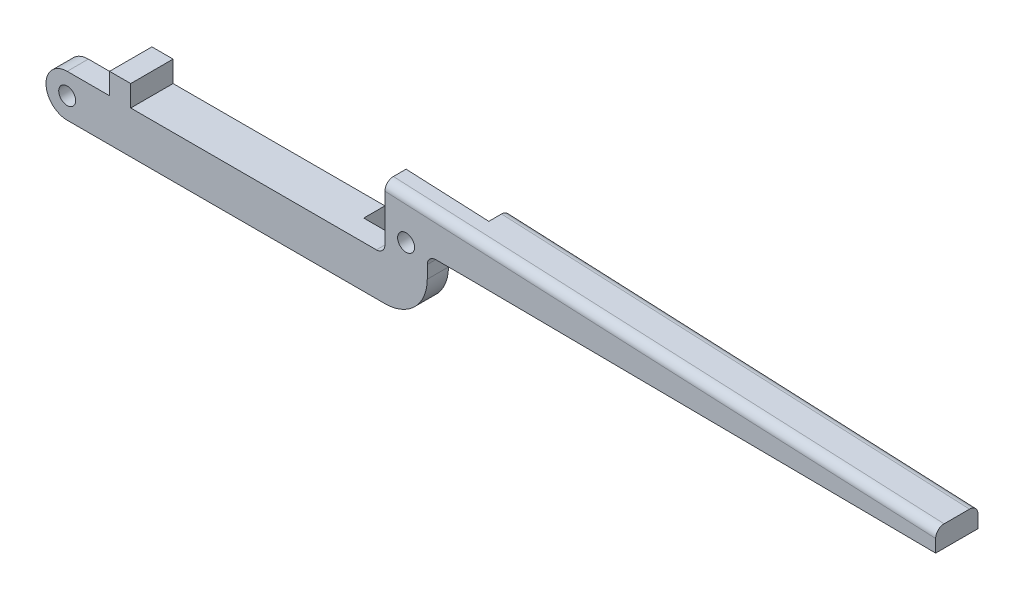
SolidWorks part; units mm, degrees
material "ABS"
ref_plane "Front Plane" through (0, 0, 0) normal (0, 0, 1) x (1, 0, 0)
ref_plane "Top Plane" through (0, 0, 0) normal (0, 1, 0) x (1, 0, 0)
ref_plane "Right Plane" through (0, 0, 0) normal (1, 0, 0) x (0, 0, -1)
sketch "Sketch1" plane through (0, 0, 0) normal (0, 0, 1) x (1, 0, 0)
  line L0 (0, 0) -> (22.5, 0) construction
  line L1 (0, -1.25) -> (0, -3.75)
  line L2 (0, -3.75) -> (20, -3.75)
  line L3 (20, 0) -> (20, 2.5)
  line L4 (-979.3777, 1.25) -> (22.9348, 1.25) construction
  line L8 (22.5, 0) -> (22.5, -3.75)
  line L9 (0, -1.25) -> (20, -1.25)
  line L10 (20, -1.25) -> (20, 0)
  line L11 (20, -3.75) -> (22.5, -3.75)
  line L12 (50, 1.25) -> (1066.376, 1.25) construction
  line L13 (22.5, 0) -> (50, 0) construction
  line L14 (22.5, 1.25) -> (50, 1.25) construction
  line L15 (22.5, 0) -> (52.5, 0)
  line L16 (52.5, 0) -> (52.5, 1)
  line L17 (52.5, 1) -> (20, 2.5)
  point P1 (0, -1.25)
  point P2 (20, 1.25)
  point P4 (0, 1.25)
  point P10 (52.5, 0)
  point P14 (52.5, 1)
  point P15 (22.5, 1.25)
  point P22 (20, 2.5)
  dimension "D1" = 1.25
  dimension "D2" = 1.25
  dimension "D3" = 2.5
  dimension "D4" = 20
  dimension "D5" = 30
  dimension "D6" = 1.25
  dimension "D7" = 2.5
  dimension "D8" = 1
  dimension "D9" = 2.5
  dimension "D10" = 5
extrude "Boss-Extrude1" add sketch "Sketch1" along normal blind 2.5
sketch "Sketch2" plane through (0, 0, 2.5) normal (0, 0, 1) x (1, 0, 0)
  line L0 (0, -3.75) -> (22.5, -3.75) construction
  line L1 (22.5, -3.75) -> (20, -3.75)
  line L2 (22.5, -3.75) -> (22.5, 2.5)
  line L3 (22.5, 2.5) -> (20, 2.5)
  line L4 (20, -3.75) -> (20, 2.5)
  line L5 (0, -1.25) -> (2.5, -1.25)
  line L6 (0, -1.25) -> (0, -3.75)
  line L7 (0, -3.75) -> (2.5, -3.75)
  line L8 (2.5, -1.25) -> (2.5, -3.75)
  dimension "D1" = 2.5
extrude "Cut-Extrude1" cut sketch "Sketch2" against normal blind 1.25
sketch "Sketch3" plane through (0, 0, 1.25) normal (0, 0, 1) x (1, 0, 0)
  line L0 (0, -1.25) -> (0, -3.75) construction
  line L1 (2.5, -1.25) -> (0, -1.25) construction
  line L2 (20, 2.5) -> (20, -1.25) construction
  line L3 (20, -3.75) -> (22.5, -3.75) construction
  circle A0 centre (1.25, -2.5) radius 0.5
  circle A1 centre (21.25, 0) radius 0.5
  point P0 (0, -2.5)
  point P1 (1.25, -1.25)
  point P4 (1.25, -2.5)
  point P9 (20, 0)
  point P10 (21.25, 0)
  dimension "D1" = 1
  dimension "D6" = 1
  dimension "D2" = 1.25
  dimension "D3" = 3.75
  dimension "D4" = 1.25
  dimension "D5" = 1.25
extrude "Cut-Extrude2" cut sketch "Sketch3" against normal through all
sketch "Sketch4" plane through (0, 0, 1.25) normal (0, 0, 1) x (1, 0, 0)
  line L1 (0, -3.75) -> (2.5, -3.75)
  line L2 (0, -3.75) -> (0, -1.25)
  line L3 (0, -1.25) -> (2.5, -1.25)
  line L4 (2.5, -3.75) -> (2.5, -1.25)
  line L5 (20, -3.75) -> (22.5, -3.75)
  line L6 (20, -3.75) -> (20, 2.3846)
  line L7 (20, 2.3846) -> (22.5, 2.3846)
  line L8 (22.5, -3.75) -> (22.5, 2.3846)
  circle A0 centre (1.25, -2.5) radius 0.5
  circle A1 centre (21.25, 0) radius 0.5
extrude "Boss-Extrude2" add sketch "Sketch4" along normal up to surface (1.25 mm away) up to face at (11.25, -2.5, 2.5)
sketch "Sketch5" plane through (0, 0, 1.25) normal (0, 0, 1) x (1, 0, 0)
  line L0 (20, 2.3846) -> (20, 2.5)
  line L1 (20, 2.5) -> (22.5, 2.3846)
  line L2 (22.5, 2.3846) -> (20, 2.3846)
extrude "Boss-Extrude3" add sketch "Sketch5" along normal blind 1.25
sketch "Sketch6" plane through (0, 0, 0) normal (0, 0, -1) x (-1, 0, 0)
  line L0 (-20, -1.25) -> (0, -1.25) construction
  line L1 (-22.5, -3.75) -> (-20, -3.75)
  line L2 (-22.5, -3.75) -> (-22.5, 2.5)
  line L3 (-22.5, 2.5) -> (-20, 2.5)
  line L4 (-20, -3.75) -> (-20, 2.5)
  line L5 (0, -3.75) -> (-2.5, -3.75)
  line L6 (0, -3.75) -> (0, -1.25)
  line L7 (0, -1.25) -> (-2.5, -1.25)
  line L8 (-2.5, -3.75) -> (-2.5, -1.25)
  dimension "D1" = 2.5
extrude "Cut-Extrude3" cut sketch "Sketch6" against normal blind 1.25
sketch "Sketch7" plane through (0, 0, 0) normal (0, 0, -1) x (-1, 0, 0)
  line L0 (-2.5, -1.25) -> (-2.5, -3.75) construction
  line L1 (-2.5, -3.75) -> (-2.5, -1.25)
  arc A0 (-2.5, -1.25) -> (-2.5, -3.75) centre (-2.5, -2.5) ccw
extrude "Cut-Extrude4" cut sketch "Sketch7" against normal blind 1.25
sketch "Sketch9" plane through (0, 0, 1.25) normal (0, 0, -1) x (-1, 0, 0)
  line L0 (-1.25, -1.25) -> (0, -1.25)
  line L1 (0, -1.25) -> (0, -3.75)
  line L2 (0, -3.75) -> (-1.25, -3.75)
  arc A0 (-1.25, -3.75) -> (-1.25, -1.25) centre (-1.25, -2.5) ccw
  line M2 (0, -3.75) -> (0, -1.25)
  line M3 (0, -1.25) -> (-2.5, -1.25)
  line M5 (-2.5, -3.75) -> (0, -3.75)
extrude "Cut-Extrude5" cut sketch "Sketch9" against normal blind 1.25 contours A0 L1 M3 | A0 M5 M2
sketch "Sketch10" plane through (0, 0, 0) normal (0, 0, -1) x (-1, 0, 0)
  line L0 (-22.5, 2.3846) -> (-24.8821, 2.2747)
  line L1 (-52.5, 1) -> (-22.5, 2.3846) construction
  line L2 (-22.5, 2.3846) -> (-22.5, 0)
  line L3 (-20, -3.75) -> (-20, -1.25)
  line L4 (-20, -1.25) -> (-17.5, -1.25)
  arc A0 (-24.8821, 2.2747) -> (-22.5, 0) centre (-22.5, 2.3846) ccw
  arc A1 (-20, -3.75) -> (-17.5, -1.25) centre (-20, -1.25) ccw
extrude "Cut-Extrude6" cut sketch "Sketch10" against normal blind 1.25
sketch "Sketch11" plane through (0, 0, 1.25) normal (0, 0, -1) x (-1, 0, 0)
  line L0 (-22.5, 0) -> (-22.5, -3.75) construction
  line L1 (-22.5, -1.25) -> (-22.5, -3.75)
  line L2 (-22.5, -3.75) -> (-20, -3.75)
  arc A0 (-22.5, -1.25) -> (-20, -3.75) centre (-20, -1.25) ccw
  point P0 (-20, -1.25)
  point P1 (-22.5, -1.25)
extrude "Cut-Extrude7" cut sketch "Sketch11" against normal blind 1.25
sketch "Sketch12" plane through (0, 0, 0) normal (0, 0, -1) x (-1, 0, 0)
  line L0 (-24.8821, 2.2747) -> (-24.8821, 0)
  line L1 (-22.5, 0) -> (-52.5, 0) construction
  line L2 (-24.8821, 0) -> (-22.5, 0)
  arc A0 (-22.5, 0) -> (-24.8821, 2.2747) centre (-22.5, 2.3846) cw
extrude "Cut-Extrude8" cut sketch "Sketch12" against normal blind 1.25
sketch "Sketch13" plane through (0, 0, 1.25) normal (0, 0, -1) x (-1, 0, 0)
  line L0 (-1.25, -1.25) -> (-2.5, -1.25) construction
  line L1 (-2.5, -3.75) -> (-1.25, -3.75) construction
  line L3 (-2.5, -1.25) -> (-2, -1.25)
  line L4 (-2, -3.75) -> (-2.5, -3.75)
  arc A0 (-2, -3.75) -> (-2, -1.25) centre (-0.6875, -2.5) cw
  arc A1 (-2.5, -1.25) -> (-2.5, -3.75) centre (-2.5, -2.5) ccw
  point P0 (-2, -1.25)
  point P1 (-2, -3.75)
  dimension "D1" = 0.5
extrude "Boss-Extrude4" add sketch "Sketch13" along normal blind 1.25
sketch "Sketch14" plane through (0, 0, 0) normal (0, 0, -1) x (-1, 0, 0)
  line L0 (-17.5, -1.25) -> (-17.5, -3.75)
  line L1 (-2, -3.75) -> (-20, -3.75) construction
  line L2 (-17.5, -3.75) -> (-20, -3.75)
  arc A0 (-20, -3.75) -> (-17.5, -1.25) centre (-20, -1.25) ccw construction
  arc A1 (-20, -3.75) -> (-17.5, -1.25) centre (-20, -1.25) ccw
  point P0 (-17.5, -1.25)
extrude "Cut-Extrude9" cut sketch "Sketch14" against normal blind 1.25
fillet "Fillet2" radius 0.5 2 edges at (38.691, 1.6373, 0) (36.25, 1.75, 2.5)
fillet "Fillet3" radius 0.5 1 edges at (22.5, 0, 1.875)
fillet "Fillet4" radius 0.5 1 edges at (20, -1.25, 1.875)
sketch "Sketch15" plane through (0, 0, 0) normal (0, 0, -1) x (-1, 0, 0)
  line L0 (-17.5, -1.25) -> (-2, -1.25) construction
  line L1 (-2, -3.75) -> (-17.5, -3.75) construction
  line L2 (-2, -3.75) -> (-2.5, -3.75)
  line L3 (-2.5, -3.75) -> (-2.5, -1.25)
  line L4 (-2.5, -1.25) -> (-2, -1.25)
  arc A0 (-2, -1.25) -> (-2, -3.75) centre (-0.6875, -2.5) ccw construction
  arc A1 (-2, -1.25) -> (-2, -3.75) centre (-0.6875, -2.5) ccw
  point P0 (-2.5, -2.5)
  point P1 (-2.5, -1.25)
  point P5 (-2.5, -3.75)
  line M5 (-2, -1.25) -> (-17.5, -1.25)
  line M7 (-17.5, -3.75) -> (-2, -3.75)
  arc M8 (-2, -3.75) -> (-2, -1.25) centre (-0.6875, -2.5) cw
extrude "Cut-Extrude10" cut sketch "Sketch15" against normal blind 1.25 contours L3 M8 M5 | L3 M7 M8
sketch "Sketch16" plane through (0, -1.25, 0) normal (0, 1, 0) x (1, 0, 0)
  line L0 (19.5, -2.5) -> (1.25, -2.5) construction
  line L1 (2.5, 0) -> (5, 0)
  line L2 (2.5, 0) -> (2.5, -2.5)
  line L3 (2.5, -2.5) -> (5, -2.5)
  line L4 (5, 0) -> (5, -2.5)
  dimension "D1" = 2.5
extrude "Boss-Extrude5" add sketch "Sketch16" along normal blind 1.25
sketch "Sketch17" plane through (0, 0, 0) normal (0, -1, 0) x (1, 0, 0)
  line L1 (52.5, 2.5) -> (24.8821, 2.5)
  line L2 (52.5, 2.5) -> (52.5, 0)
  line L3 (52.5, 0) -> (24.8821, 0)
  line L4 (24.8821, 2.5) -> (24.8821, 0)
extrude "Boss-Extrude6" add sketch "Sketch17" along normal blind 0.25
sketch "Sketch18" plane through (0, 0, 0) normal (0, 0, -1) x (-1, 0, 0)
  line L0 (-24.8821, 0) -> (-52.5, -0.25)
  line L1 (-52.5, -0.25) -> (-24.8821, -0.25)
  line L2 (-24.8821, -0.25) -> (-24.8821, 0)
extrude "Cut-Extrude11" cut sketch "Sketch18" against normal through all
sketch "Sketch19" plane through (0, 0, 0) normal (0, 0, -1) x (-1, 0, 0)
  line L0 (-5, 0) -> (-2.5, 0) construction
  line L1 (-2.5, -1.25) -> (-3.75, -1.25)
  line L2 (-2.5, -1.25) -> (-2.5, 0)
  line L3 (-2.5, 0) -> (-3.75, 0)
  line L4 (-3.75, -1.25) -> (-3.75, 0)
extrude "Cut-Extrude12" cut sketch "Sketch19" against normal through all
